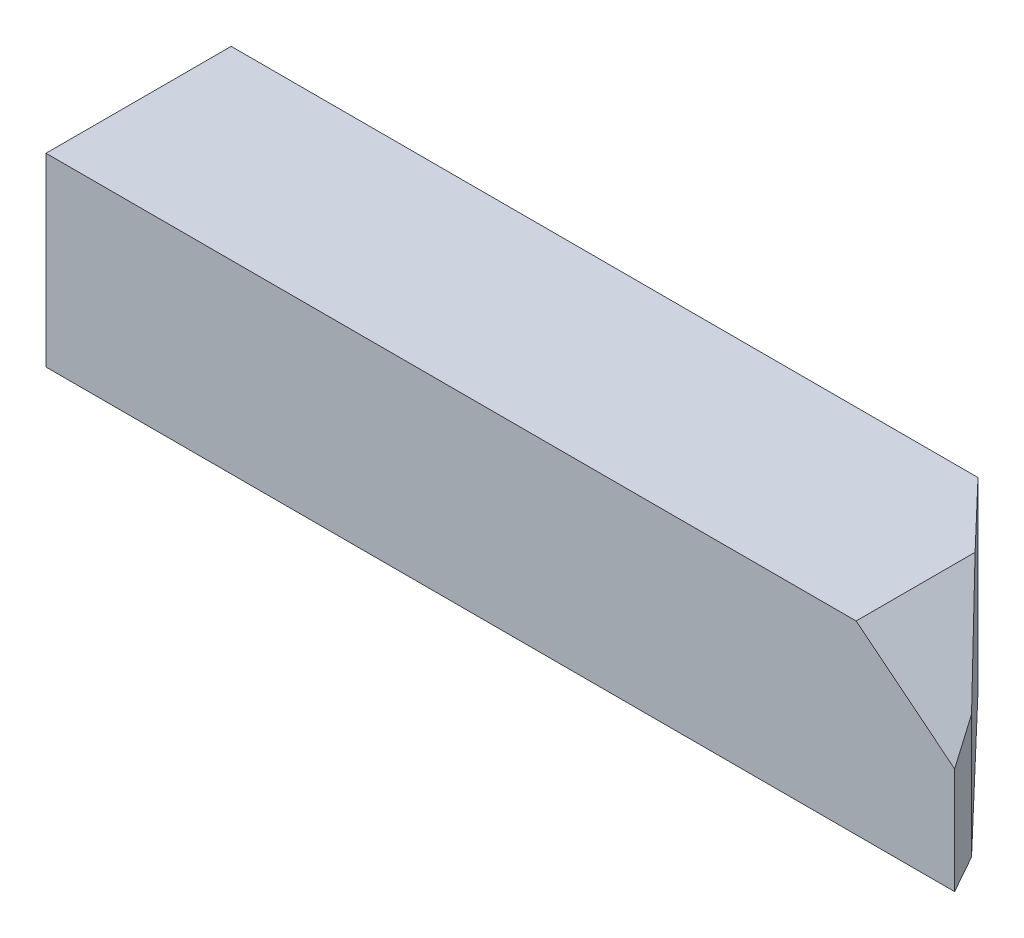
SolidWorks part; units mm, degrees
ref_plane "Спереди" through (0, 0, 0) normal (0, 0, 1) x (1, 0, 0)
ref_plane "Сверху" through (0, 0, 0) normal (0, 1, 0) x (1, 0, 0)
ref_plane "Справа" through (0, 0, 0) normal (1, 0, 0) x (0, 0, -1)
sketch "Эскиз1" plane through (0, 0, 0) normal (0, 0, 1) x (1, 0, 0)
  line L0 (0, 0) -> (0, 8)
  line L1 (0, 8) -> (35, 8)
  line L2 (35, 8) -> (39.2561, 4.5951)
  line L3 (39.2561, 4.5951) -> (39.2561, 0)
  line L4 (39.2561, 0) -> (0, 0)
extrude "Бобышка-Вытянуть1" add sketch "Эскиз1" along normal blind 8
sketch "Эскиз2" plane through (0, 0, 0) normal (0, -1, 0) x (1, 0, 0)
  line L5 (32.2656, 0) -> (39.2561, 0)
  line L6 (0, 0) -> (39.2561, 0) construction
  line L7 (39.2561, 0) -> (39.2561, 8)
  line L8 (39.2561, 8) -> (38.3252, 6.3388)
  line L9 (38.3252, 6.3388) -> (32.2656, 0)
  point P4 (38.3252, 6.3388)
extrude "Вырез-Вытянуть1" cut sketch "Эскиз2" against normal through all
